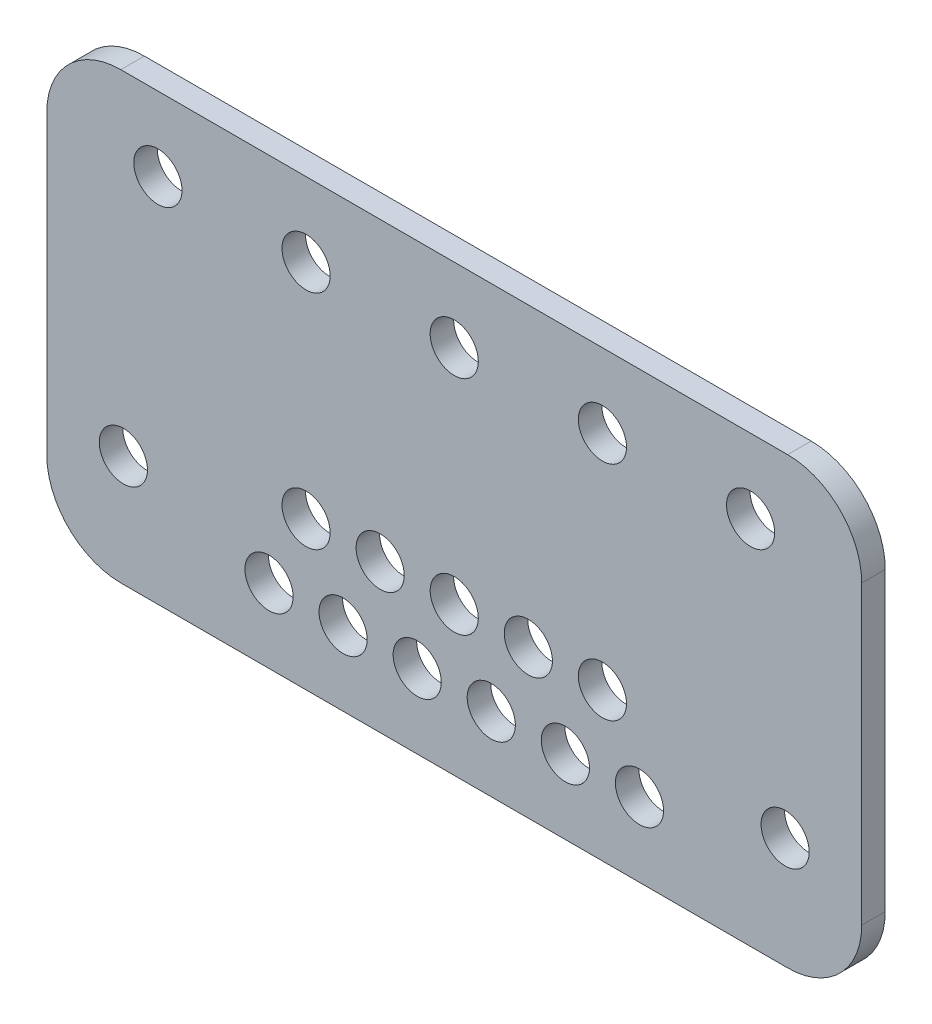
SolidWorks part; units mm, degrees
material "6061-T6 (SS)"
ref_plane "Front Plane" through (0, 0, 0) normal (0, 0, 1) x (1, 0, 0)
ref_plane "Top Plane" through (0, 0, 0) normal (0, 1, 0) x (1, 0, 0)
ref_plane "Right Plane" through (0, 0, 0) normal (1, 0, 0) x (0, 0, -1)
sketch "Sketch1" plane through (0, 0, 0) normal (0, 0, 1) x (1, 0, 0)
  line L1 (-55, -30) -> (55, -30)
  line L2 (-55, -30) -> (-55, 30)
  line L3 (-55, 30) -> (55, 30)
  line L4 (55, -30) -> (55, 30)
  line L5 (-55, -30) -> (55, 30) construction
  line L6 (-55, 30) -> (55, -30) construction
  point P0 (0, 0)
  dimension "D1" = 60
  dimension "D2" = 110
extrude "Boss-Extrude1" add sketch "Sketch1" along normal blind 3.175
sketch "Sketch2" plane through (0, 0, 3.175) normal (0, 0, 1) x (1, 0, 0)
  line L0 (-40, 20) -> (40, 20) construction
  line L1 (0, 0) -> (0, 20) construction
  line L2 (55, 30) -> (-55, 30) construction
  line L3 (40, 20) -> (40, -15) construction
  line L4 (-40, 20) -> (-40, -15) construction
  line L5 (-55, -30) -> (55, -30) construction
  line L6 (-5, -20) -> (-5, -10) construction
  line L7 (5, -20) -> (-5, -20) construction
  line L8 (-5, -20) -> (-15, -20) construction
  line L9 (5, -20) -> (5, -10) construction
  line L10 (5, -20) -> (15, -20) construction
  line L11 (-20, -10) -> (-10, -10) construction
  line L12 (-10, -10) -> (0, -10) construction
  line L13 (0, -10) -> (10, -10) construction
  line L14 (10, -10) -> (20, -10) construction
  line L15 (15, -20) -> (15, -10) construction
  line L16 (15, -20) -> (19.66, -20) construction
  line L17 (19.66, -20) -> (25, -20) construction
  line L18 (-15.34, -20) -> (-25, -20) construction
  line L19 (-55, -30) -> (55, -30) construction
  circle A0 centre (-40, 20) radius 3.25
  circle A1 centre (40, 20) radius 3.25
  circle A2 centre (-20, 20) radius 3.25
  circle A3 centre (0, 20) radius 3.25
  circle A4 centre (20, 20) radius 3.25
  circle A5 centre (44.66, -15) radius 3.25
  circle A6 centre (5, -20) radius 3.25
  circle A7 centre (44.66, -15) radius 4.66 construction
  circle A8 centre (5, -20) radius 4.66 construction
  circle A9 centre (0, -10) radius 3.25
  circle A10 centre (-5, -20) radius 3.25
  circle A11 centre (-10, -10) radius 3.25
  circle A12 centre (-15, -20) radius 3.25
  circle A13 centre (10, -10) radius 3.25
  circle A14 centre (-20, -10) radius 3.25
  circle A15 centre (-44.66, -15) radius 3.25
  circle A16 centre (-44.66, -15) radius 4.66 construction
  circle A17 centre (10, -10) radius 4.66 construction
  circle A18 centre (0, -10) radius 4.66 construction
  circle A19 centre (-10, -10) radius 4.66 construction
  circle A20 centre (-20, -10) radius 4.66 construction
  circle A21 centre (20, -10) radius 3.25
  circle A22 centre (20, -10) radius 4.66 construction
  circle A23 centre (15, -20) radius 3.25
  circle A24 centre (15, -20) radius 4.66 construction
  circle A25 centre (-15, -20) radius 4.66 construction
  circle A26 centre (-5, -20) radius 4.66 construction
  circle A27 centre (-25, -20) radius 3.25
  circle A28 centre (25, -20) radius 3.25
  circle A29 centre (-25, -20) radius 4.66 construction
  circle A30 centre (25, -20) radius 4.66 construction
  point P23 (0.34, -20)
  point P39 (9.66, -20)
  point P40 (40, -15)
  point P45 (14.66, -10)
  point P56 (19.66, -20)
  point P57 (24.66, -10)
  point P61 (-15.34, -10)
  point P62 (-14.66, -10)
  point P63 (-5.34, -10)
  point P64 (-4.66, -10)
  point P65 (-10.34, -20)
  point P66 (-9.66, -20)
  point P67 (-0.34, -20)
  point P68 (-19.66, -20)
  point P69 (-24.66, -10)
  point P70 (5.34, -10)
  point P71 (4.66, -10)
  point P72 (15.34, -10)
  point P73 (10.34, -20)
  point P83 (-29.66, -20)
  point P84 (-20, -20)
  point P85 (20.34, -20)
  point P86 (-20.34, -20)
  dimension "D1" = 6.5
  dimension "D6" = 9.32
  dimension "D2" = 80
  dimension "D3" = 10
  dimension "D4" = 40
  dimension "D5" = 15
  dimension "D7" = 10
  dimension "D8" = 20
  dimension "D9" = 50
  dimension "D10" = 10
  dimension "D11" = 15
  dimension "D12" = 60.34
  dimension "D13" = 40.34
  dimension "D14" = 50.34
extrude "Cut-Extrude1" cut sketch "Sketch2" against normal through all
fillet "Fillet1" radius 10 4 edges at (55, 30, 1.5875) (-55, 30, 1.5875) (-55, -30, 1.5875) (55, -30, 1.5875)
